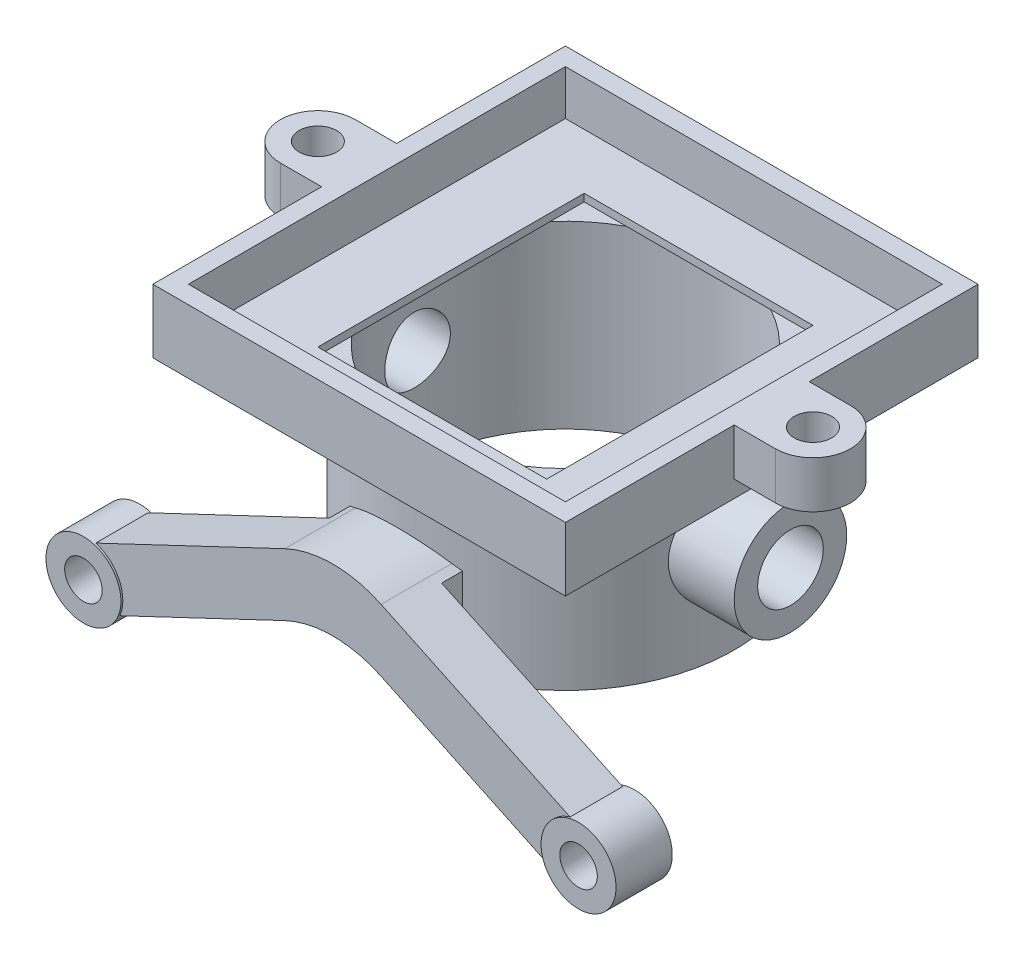
SolidWorks part; units mm, degrees
other "标注1"
sketch "草图9" plane through (7.6, 6.2, 6.25) normal (0.5685, 0.464, 0.6794) x (0.8127, -0.1883, -0.5515)
other "标注2"
sketch "草图10" plane through (-7.6, -1.8, 6.125) normal (-0.6962, -0.7148, 0.0657) x (0.1425, -0.0478, 0.9886)
ref_plane "前视基准面" through (0, 0, 0) normal (0, 0, 1) x (1, 0, 0)
ref_plane "上视基准面" through (0, 0, 0) normal (0, 1, 0) x (1, 0, 0)
ref_plane "右视基准面" through (0, 0, 0) normal (1, 0, 0) x (0, 0, -1)
sketch "草图1" plane through (0, 0, 0) normal (0, 1, 0) x (1, 0, 0)
  circle A0 centre (0, 0) radius 4
  circle A1 centre (0, 0) radius 4.5
  dimension "D1" = 8
  dimension "D2" = 9
extrude "凸台-拉伸1" add sketch "草图1" along normal blind 4.5
sketch "草图2" plane through (0, 4.5, 0) normal (0, 1, 0) x (1, 0, 0)
  line L1 (-5.5, 5.5) -> (5.5, 5.5)
  line L2 (-5.5, 5.5) -> (-5.5, -5.5)
  line L3 (-5.5, -5.5) -> (5.5, -5.5)
  line L4 (5.5, 5.5) -> (5.5, -5.5)
  line L5 (-5.5, 5.5) -> (5.5, -5.5) construction
  line L6 (-5.5, -5.5) -> (5.5, 5.5) construction
  circle A0 centre (0, 0) radius 4
  point P0 (0, 0)
  dimension "D1" = 11
  dimension "D2" = 11
extrude "凸台-拉伸2" add sketch "草图2" along normal blind 0.5
sketch "草图3" plane through (0, 5, 0) normal (0, 1, 0) x (1, 0, 0)
  line L1 (-3.05, 3.55) -> (3.05, 3.55)
  line L2 (-3.05, 3.55) -> (-3.05, -3.55)
  line L3 (-3.05, -3.55) -> (3.05, -3.55)
  line L4 (3.05, 3.55) -> (3.05, -3.55)
  line L5 (-3.05, 3.55) -> (3.05, -3.55) construction
  line L6 (-3.05, -3.55) -> (3.05, 3.55) construction
  point P0 (0, 0)
  dimension "D1" = 6.1
  dimension "D2" = 7.1
extrude "切除-拉伸1" cut sketch "草图3" against normal blind 0.2
sketch "草图4" plane through (0, 5, 0) normal (0, 1, 0) x (1, 0, 0)
  line L1 (-5.025, 5.025) -> (5.025, 5.025)
  line L2 (-5.025, 5.025) -> (-5.025, -5.025)
  line L3 (-5.025, -5.025) -> (5.025, -5.025)
  line L4 (5.025, 5.025) -> (5.025, -5.025)
  line L5 (-5.025, 5.025) -> (5.025, -5.025) construction
  line L6 (-5.025, -5.025) -> (5.025, 5.025) construction
  line L7 (-5.5, 5.5) -> (5.5, 5.5)
  line L8 (-5.5, 5.5) -> (-5.5, -5.5)
  line L9 (-5.5, -5.5) -> (5.5, -5.5)
  line L10 (5.5, 5.5) -> (5.5, -5.5)
  line L11 (-5.5, 5.5) -> (5.5, -5.5) construction
  line L12 (-5.5, -5.5) -> (5.5, 5.5) construction
  point P0 (0, 0)
  point P6 (0, 0)
  dimension "D1" = 10.05
  dimension "D2" = 10.05
extrude "凸台-拉伸3" add sketch "草图4" along normal blind 1.2
sketch "草图5" plane through (0, 6.2, 0) normal (0, 1, 0) x (1, 0, 0)
  line L0 (5.5, -5.5) -> (5.5, 5.5) construction
  line L1 (0, 0) -> (0, 1.6001) construction
  line L2 (5.5, 1) -> (6.6, 1)
  line L3 (5.5, 1) -> (5.5, -1)
  line L4 (5.5, -1) -> (6.6, -1)
  line L6 (0, 0) -> (5.5, 0) construction
  line L7 (-5.5, -1) -> (-6.6, -1)
  line L8 (-5.5, 1) -> (-6.6, 1)
  arc A0 (6.6, 1) -> (6.6, -1) centre (6.6, 0) cw
  circle A1 centre (6.6, 0) radius 0.5
  arc A2 (-6.6, 1) -> (-6.6, -1) centre (-6.6, 0) ccw
  circle A3 centre (-6.6, 0) radius 0.5
  dimension "D3" = 1
  dimension "D1" = 2
  dimension "D2" = 1.1
extrude "凸台-拉伸4" add sketch "草图5" against normal blind 1.25 contours A0 L2 L1 L4 A1 | L8 A2 L7 L0 A3
sketch "草图6" plane through (0, 0, 5.5) normal (0, 0, 1) x (1, 0, 0)
  line L0 (-5.5, 6.2) -> (5.5, 6.2) construction
  line L1 (0, 0) -> (0, -2.1044) construction
  circle A0 centre (-6.6, -0.8) radius 0.5
  circle A2 centre (-6.6, -0.8) radius 1
  circle A3 centre (6.6, -0.8) radius 1
  circle A4 centre (6.6, -0.8) radius 0.5
  dimension "D3" = 2
  dimension "D4" = 1
  dimension "D1" = 7
  dimension "D2" = 13.2
extrude "凸台-拉伸5" add sketch "草图6" along normal mid plane 1.5 separate body
sketch "草图7" plane through (0, 0, 5.5) normal (0, 0, 1) x (1, 0, 0)
  line L0 (-6.4696, 0.0919) -> (0, 3.1601)
  line L1 (-6.4696, 0.0919) -> (-5.8269, -1.2634)
  line L2 (-5.8269, -1.2634) -> (0, 1.5)
  line L3 (-6.1482, -0.5857) -> (-6.6, -0.8) construction
  line L4 (0, 1.5) -> (0, 0) construction
  line L5 (0, 3.1601) -> (0, 1.5) construction
  line L12 (-5.1543, -0.1144) -> (-6.1482, -0.5857) construction
  line L45 (6.4696, 0.0919) -> (5.8269, -1.2634)
  line L46 (5.8269, -1.2634) -> (0, 1.5)
  line L47 (6.4696, 0.0919) -> (0, 3.1601)
  circle A0 centre (-6.6, -0.8) radius 0.5 construction
  dimension "D1" = 1.5
  dimension "D2" = 1.5
extrude "凸台-拉伸6" add sketch "草图7" along normal mid plane 1.4
fillet "圆角1" radius 3 2 edges at (0, 1.5, 5.5) (0, 3.1601, 5.5)
sketch "草图8" plane through (0, 0, 4.8) normal (0, 0, -1) x (-1, 0, 0)
  line L0 (0, 0) -> (0, 0.8484) construction
  line L1 (1.5, 2.4488) -> (1.5, 0.7886)
  line L2 (-1.5, 2.4488) -> (-1.5, 0.7886)
  line L3 (-1.5, 2.4488) -> (1.5, 2.4488) construction
  line L4 (6.3237, 0.1611) -> (1.2855, 2.5505)
  line L5 (-1.2855, 2.5505) -> (-6.3237, 0.1611)
  line L6 (-5.681, -1.1942) -> (-1.2855, 0.8903)
  line L7 (1.2855, 0.8903) -> (5.681, -1.1942)
  line L8 (1.5, 2.4488) -> (1.2855, 2.5505)
  line L9 (-1.2855, 2.5505) -> (-1.5, 2.4488)
  line L10 (-1.5, 0.7886) -> (-1.2855, 0.8903)
  line L11 (1.2855, 0.8903) -> (1.5, 0.7886)
  arc A4 (1.2855, 2.5505) -> (-1.2855, 2.5505) centre (0, -0.1601) ccw
  arc A6 (1.2855, 0.8903) -> (-1.2855, 0.8903) centre (0, -1.8203) ccw
  arc A8 (1.2855, 2.5505) -> (-1.2855, 2.5505) centre (0, -0.1601) ccw
  arc A10 (1.2855, 0.8903) -> (-1.2855, 0.8903) centre (0, -1.8203) ccw
  arc A11 (-5.681, -1.1942) -> (-6.3237, 0.1611) centre (-6.6, -0.8) ccw
  arc A12 (6.3237, 0.1611) -> (5.681, -1.1942) centre (6.6, -0.8) ccw
  dimension "D2" = 3
  dimension "D1" = 0
extrude "凸台-拉伸7" add sketch "草图8" along normal blind 0.9
sketch "草图11" plane through (0, 5, 0) normal (0, 1, 0) x (1, 0, 0)
  line L0 (-3.05, -2.588) -> (-3.05, -3.55) construction
  line L1 (-3.05, 2.588) -> (-3.05, -2.588)
  line L2 (0, 0) -> (0, 1.4928) construction
  line L3 (3.05, 2.588) -> (3.05, -2.588)
  line L4 (3.05, 3.55) -> (1.8432, 3.55) construction
  line L5 (-1.8432, 3.55) -> (1.8432, 3.55)
  line L6 (0, 0) -> (1.1655, 0) construction
  line L7 (-1.8432, -3.55) -> (1.8432, -3.55)
  arc A0 (-3.05, 2.588) -> (-3.05, -2.588) centre (0, 0) ccw
  arc A1 (3.05, 2.588) -> (3.05, -2.588) centre (0, 0) cw
  arc A2 (-1.8432, 3.55) -> (1.8432, 3.55) centre (0, 0) cw
  arc A3 (-1.8432, -3.55) -> (1.8432, -3.55) centre (0, 0) ccw
extrude "凸台-拉伸8" add sketch "草图11" against normal blind 0.2
sketch "草图12" plane through (0, 0, 0) normal (0, -1, 0) x (1, 0, 0)
  circle A0 centre (0, 0) radius 4.5
extrude "切除-拉伸2" cut sketch "草图12" against normal blind 0.001
sketch "草图13" plane through (0, 0.001, 0) normal (0, -1, 0) x (1, 0, 0)
  circle A0 centre (0, 0) radius 4.0375
  dimension "D1" = 8.075
extrude "切除-拉伸3" cut sketch "草图13" against normal up to surface (4.799 mm away) up to face at (3.525, 4.8, 0)
sketch "草图19" plane through (0, 0, 0) normal (0, 1, 0) x (1, 0, 0)
  line L0 (0, 0) -> (-6, 0) construction
  line L1 (-0.2112, 0) -> (-1.9817, 0) construction
  dimension "D1" = 0
  dimension "D2" = 6
ref_plane "基准面1" through (-6, 0, 0) normal (-1, 0, 0) x (0, 0, 1)
sketch "草图20" plane through (-6, 0, 0) normal (-1, 0, 0) x (0, 0, 1)
  circle A0 centre (0, 2.6578) radius 1.5
  dimension "D1" = 3
extrude "凸台-拉伸10" add sketch "草图20" against normal blind 1.8
sketch "草图21" plane through (-6, 0, 0) normal (-1, 0, 0) x (0, 0, 1)
  circle A0 centre (0, 2.6578) radius 0.875
  dimension "D1" = 1.75
extrude "切除-拉伸5" cut sketch "草图21" against normal blind 3
mirror "镜向3" about plane through (0, 0, 0) normal (1, 0, 0) of "凸台-拉伸10", "切除-拉伸5"
